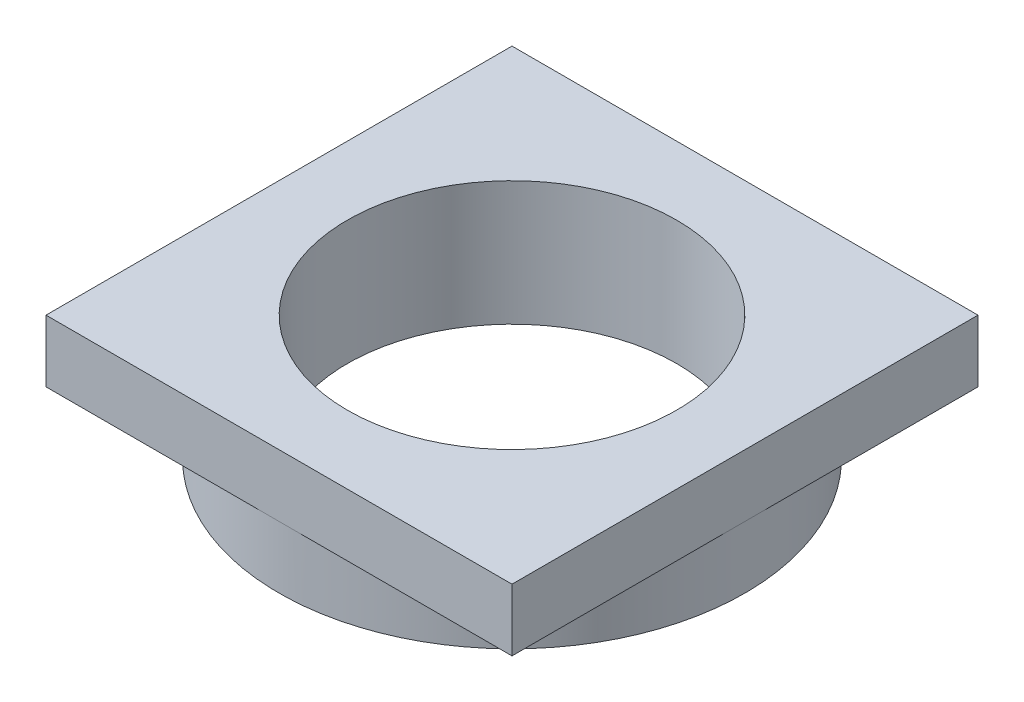
SolidWorks part; units mm, degrees
ref_plane "Front Plane" through (0, 0, 0) normal (0, 0, 1) x (1, 0, 0)
ref_plane "Top Plane" through (0, 0, 0) normal (0, 1, 0) x (1, 0, 0)
ref_plane "Right Plane" through (0, 0, 0) normal (1, 0, 0) x (0, 0, -1)
sketch "Sketch1" plane through (0, 0, 0) normal (0, 1, 0) x (1, 0, 0)
  line L1 (-37.5, -37.5) -> (37.5, -37.5)
  line L2 (-37.5, -37.5) -> (-37.5, 37.5)
  line L3 (-37.5, 37.5) -> (37.5, 37.5)
  line L4 (37.5, -37.5) -> (37.5, 37.5)
  line L5 (-37.5, -37.5) -> (37.5, 37.5) construction
  line L6 (-37.5, 37.5) -> (37.5, -37.5) construction
  circle A0 centre (0, 0) radius 26.5
  point P0 (0, 0)
  dimension "D3" = 53
  dimension "D1" = 75
  dimension "D2" = 75
extrude "Boss-Extrude1" add sketch "Sketch1" along normal blind 10
sketch "Sketch2" plane through (0, 0, 0) normal (0, -1, 0) x (1, 0, 0)
  circle A0 centre (0, 0) radius 26.5 construction
  circle A1 centre (0, 0) radius 26.5
  circle A2 centre (0, 0) radius 37.5
extrude "Boss-Extrude2" add sketch "Sketch2" along normal blind 10
